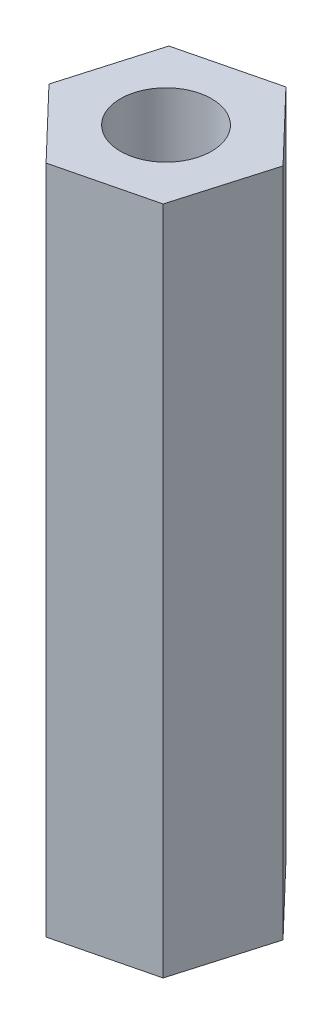
SolidWorks part; units mm, degrees
ref_plane "Front Plane" through (0, 0, 0) normal (0, 0, 1) x (1, 0, 0)
ref_plane "Top Plane" through (0, 0, 0) normal (0, 1, 0) x (1, 0, 0)
ref_plane "Right Plane" through (0, 0, 0) normal (1, 0, 0) x (0, 0, -1)
sketch "Sketch1" plane through (0, 0, 0) normal (0, 1, 0) x (1, 0, 0)
  line L1 (-2.7677, 3.3349) -> (-1.7448, 6.8555)
  line L2 (-1.7448, 6.8555) -> (-4.2822, 9.5017)
  line L3 (-4.2822, 9.5017) -> (-7.8426, 8.6273)
  line L4 (-7.8426, 8.6273) -> (-8.8655, 5.1067)
  line L5 (-8.8655, 5.1067) -> (-6.3281, 2.4605)
  line L6 (-6.3281, 2.4605) -> (-2.7677, 3.3349)
  circle A0 centre (-5.3052, 5.9811) radius 3.175 construction
  dimension "D1" = 6.35
extrude "Boss-Extrude1" add sketch "Sketch1" along normal blind 25.4
sketch "Sketch3" plane through (0, 0, 0) normal (0, -1, 0) x (1, 0, 0)
  line L0 (-4.2822, -9.5017) -> (-6.3281, -2.4605) construction
  circle A0 centre (-5.3052, -5.9811) radius 1.7272
  dimension "D1" = 3.4544
extrude "Cut-Extrude2" cut sketch "Sketch3" against normal through all
